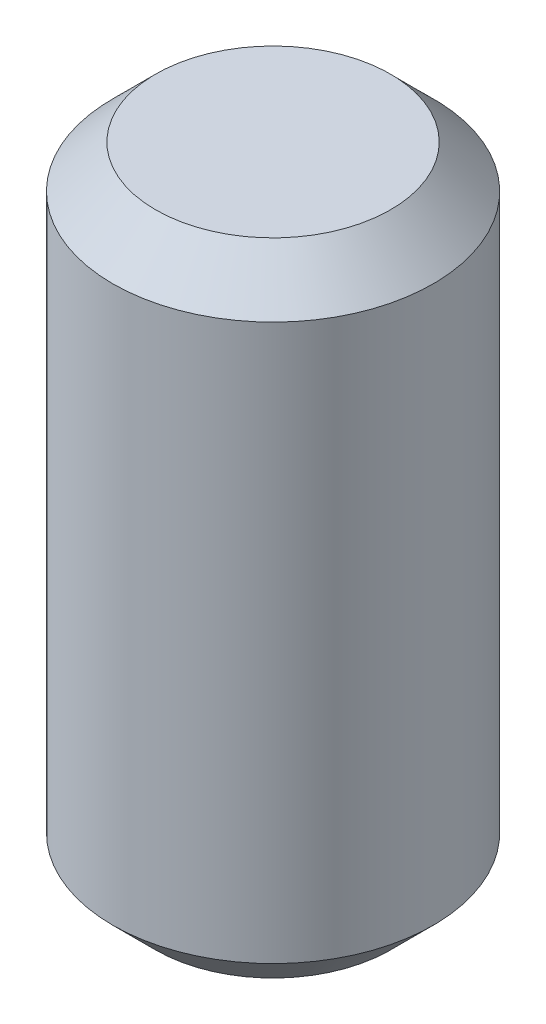
SolidWorks part; units mm, degrees
ref_plane "Front Plane" through (0, 0, 0) normal (0, 0, 1) x (1, 0, 0)
ref_plane "Top Plane" through (0, 0, 0) normal (0, 1, 0) x (1, 0, 0)
ref_plane "Right Plane" through (0, 0, 0) normal (1, 0, 0) x (0, 0, -1)
sketch "Sketch1" plane through (0, 0, 0) normal (0, 1, 0) x (1, 0, 0)
  circle A0 centre (0, 0) radius 7.5
  dimension "D1" = 15
extrude "Boss-Extrude1" add sketch "Sketch1" along normal mid plane 30
chamfer "Chamfer2" distance 2 angle 45 2 edges at (0, -15, 7.5) (0, 15, 7.5)
